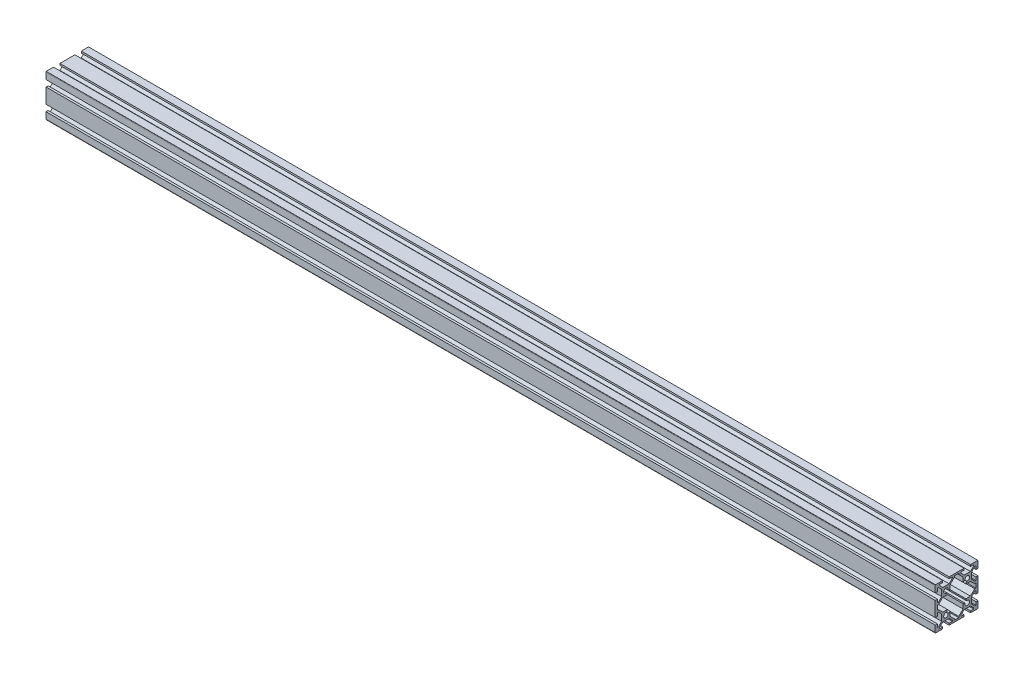
SolidWorks part; units mm, degrees
ref_plane "Front Plane" through (0, 0, 0) normal (0, 0, 1) x (1, 0, 0)
ref_plane "Top Plane" through (0, 0, 0) normal (0, 1, 0) x (1, 0, 0)
ref_plane "Right Plane" through (0, 0, 0) normal (1, 0, 0) x (0, 0, -1)
sketch "Sketch1" plane through (0, 0, 0) normal (1, 0, 0) x (0, 0, -1)
  line L0 (-16.9393, 2) -> (-18, 2)
  line L1 (-12.9393, 6) -> (-16.9393, 2)
  line L2 (-8.6667, 6) -> (-12.9393, 6)
  line L3 (-9.3359, 8.0078) -> (-8.6667, 6)
  line L4 (-6, 8.6667) -> (-8.0078, 9.3359)
  line L5 (-6, 12.9393) -> (-6, 8.6667)
  line L6 (-2, 16.9393) -> (-6, 12.9393)
  line L7 (-2, 18) -> (-2, 16.9393)
  line L8 (2, 18) -> (-2, 18)
  line L9 (2, 16.9393) -> (2, 18)
  line L10 (6, 12.9393) -> (2, 16.9393)
  line L11 (6, 8.6667) -> (6, 12.9393)
  line L12 (8.0078, 9.3359) -> (6, 8.6667)
  line L13 (8.6667, 6) -> (9.3359, 8.0078)
  line L14 (12.9393, 6) -> (8.6667, 6)
  line L15 (16.9393, 2) -> (12.9393, 6)
  line L16 (18, 2) -> (16.9393, 2)
  line L17 (18, -2) -> (18, 2)
  line L18 (16.9393, -2) -> (18, -2)
  line L19 (12.9393, -6) -> (16.9393, -2)
  line L20 (8.6667, -6) -> (12.9393, -6)
  line L21 (9.3359, -8.0078) -> (8.6667, -6)
  line L22 (6, -8.6667) -> (8.0078, -9.3359)
  line L23 (6, -12.9393) -> (6, -8.6667)
  line L24 (2, -16.9393) -> (6, -12.9393)
  line L25 (2, -18) -> (2, -16.9393)
  line L26 (-2, -18) -> (2, -18)
  line L27 (-2, -16.9393) -> (-2, -18)
  line L28 (-6, -12.9393) -> (-2, -16.9393)
  line L29 (-6, -8.6667) -> (-6, -12.9393)
  line L30 (-8.0078, -9.3359) -> (-6, -8.6667)
  line L31 (-8.6667, -6) -> (-9.3359, -8.0078)
  line L32 (-12.9393, -6) -> (-8.6667, -6)
  line L33 (-16.9393, -2) -> (-12.9393, -6)
  line L34 (-18, -2) -> (-16.9393, -2)
  line L35 (-18, 2) -> (-18, -2)
  line L36 (-20, 19) -> (-20, 13)
  line L37 (-20, 13) -> (-18, 13)
  line L38 (-18, 13) -> (-18, 16)
  line L39 (-18, 16) -> (-17.0607, 16)
  line L40 (-17.0607, 16) -> (-14, 12.9393)
  line L41 (-14, 12.9393) -> (-14, 7.0607)
  line L45 (-14, 7.0607) -> (-17.0607, 4)
  line L46 (-17.0607, 4) -> (-18, 4)
  line L47 (-18, 4) -> (-18, 7)
  line L48 (-18, 7) -> (-20, 7)
  line L49 (-20, 7) -> (-20, -7)
  line L50 (-20, -7) -> (-18, -7)
  line L51 (-18, -7) -> (-18, -4)
  line L52 (-18, -4) -> (-17.0607, -4)
  line L53 (-17.0607, -4) -> (-14, -7.0607)
  line L54 (-14, -7.0607) -> (-14, -12.9393)
  line L58 (-14, -12.9393) -> (-17.0607, -16)
  line L59 (-17.0607, -16) -> (-18, -16)
  line L60 (-18, -16) -> (-18, -13)
  line L61 (-18, -13) -> (-20, -13)
  line L62 (-20, -13) -> (-20, -19)
  line L63 (-19.8, -19.6) -> (-13, -19.6)
  line L64 (-13, -19.6) -> (-13, -18)
  line L65 (-13, -18) -> (-16, -18)
  line L66 (-16, -18) -> (-16, -17.0607)
  line L67 (-16, -17.0607) -> (-12.9393, -14)
  line L68 (-12.9393, -14) -> (-7.0607, -14)
  line L72 (-7.0607, -14) -> (-4, -17.0607)
  line L73 (-4, -17.0607) -> (-4, -18)
  line L74 (-4, -18) -> (-7, -18)
  line L75 (-7, -18) -> (-7, -19.6)
  line L76 (-7, -19.6) -> (7, -19.6)
  line L77 (7, -19.6) -> (7, -18)
  line L78 (7, -18) -> (4, -18)
  line L79 (4, -18) -> (4, -17.0607)
  line L80 (4, -17.0607) -> (7.0607, -14)
  line L81 (7.0607, -14) -> (12.9393, -14)
  line L85 (12.9393, -14) -> (16, -17.0607)
  line L86 (16, -17.0607) -> (16, -18)
  line L87 (16, -18) -> (13, -18)
  line L88 (13, -18) -> (13, -19.6)
  line L89 (13, -19.6) -> (19.8, -19.6)
  line L90 (20, -19) -> (20, -13)
  line L91 (20, -13) -> (18, -13)
  line L92 (18, -13) -> (18, -16)
  line L93 (18, -16) -> (17.0607, -16)
  line L94 (17.0607, -16) -> (14, -12.9393)
  line L98 (14, -12.9393) -> (14, -7.0607)
  line L99 (14, -7.0607) -> (17.0607, -4)
  line L100 (17.0607, -4) -> (18, -4)
  line L101 (18, -4) -> (18, -7)
  line L102 (18, -7) -> (20, -7)
  line L103 (20, -7) -> (20, 7)
  line L104 (20, 7) -> (18, 7)
  line L105 (18, 7) -> (18, 4)
  line L106 (18, 4) -> (17.0607, 4)
  line L107 (17.0607, 4) -> (14, 7.0607)
  line L111 (14, 7.0607) -> (14, 12.9393)
  line L112 (14, 12.9393) -> (17.0607, 16)
  line L113 (17.0607, 16) -> (18, 16)
  line L114 (18, 16) -> (18, 13)
  line L115 (18, 13) -> (20, 13)
  line L116 (20, 13) -> (20, 19)
  line L117 (19.8, 19.6) -> (13, 19.6)
  line L118 (13, 19.6) -> (13, 18)
  line L119 (13, 18) -> (16, 18)
  line L120 (16, 18) -> (16, 17.0607)
  line L121 (16, 17.0607) -> (12.9393, 14)
  line L125 (12.9393, 14) -> (7.0607, 14)
  line L126 (7.0607, 14) -> (4, 17.0607)
  line L127 (4, 17.0607) -> (4, 18)
  line L128 (4, 18) -> (7, 18)
  line L129 (7, 18) -> (7, 19.6)
  line L130 (7, 19.6) -> (-7, 19.6)
  line L131 (-7, 19.6) -> (-7, 18)
  line L132 (-7, 18) -> (-4, 18)
  line L133 (-4, 18) -> (-4, 17.0607)
  line L134 (-4, 17.0607) -> (-7.0607, 14)
  line L138 (-7.0607, 14) -> (-12.9393, 14)
  line L139 (-12.9393, 14) -> (-16, 17.0607)
  line L140 (-16, 17.0607) -> (-16, 18)
  line L141 (-16, 18) -> (-13, 18)
  line L142 (-13, 18) -> (-13, 19.6)
  line L143 (-13, 19.6) -> (-19.8, 19.6)
  arc A0 (-20, -19) -> (-19.8, -19.6) centre (-19, -19) ccw
  arc A1 (19.8, -19.6) -> (20, -19) centre (19, -19) ccw
  arc A2 (20, 19) -> (19.8, 19.6) centre (19, 19) ccw
  arc A3 (-19.8, 19.6) -> (-20, 19) centre (-19, 19) ccw
  arc A4 (-8.0078, 9.3359) -> (-9.3359, 8.0078) centre (-10, 10) ccw
  arc A5 (9.3359, 8.0078) -> (8.0078, 9.3359) centre (10, 10) ccw
  arc A6 (8.0078, -9.3359) -> (9.3359, -8.0078) centre (10, -10) ccw
  arc A7 (-9.3359, -8.0078) -> (-8.0078, -9.3359) centre (-10, -10) ccw
  dimension "A" = 40
  dimension "T" = 39.2
extrude "Boss-Extrude1" add sketch "Sketch1" along normal blind 832
ref_plane "Plane1" through (0, 19.6, 0) normal (0, 1, 0) x (1, 0, 0)
ref_plane "Plane2" through (0, 0, 0) normal (1, 0, 0) x (0, 0, -1)
ref_plane "Plane3" through (832, 0, 0) normal (1, 0, 0) x (0, 0, -1)
ref_plane "Plane4" through (7, 0, 0) normal (1, 0, 0) x (0, 0, -1)
ref_plane "Plane5" through (19, 0, 0) normal (1, 0, 0) x (0, 0, -1)
ref_plane "Plane6" through (31, 0, 0) normal (1, 0, 0) x (0, 0, -1)
ref_plane "Plane7" through (43, 0, 0) normal (1, 0, 0) x (0, 0, -1)
ref_plane "Plane8" through (55, 0, 0) normal (1, 0, 0) x (0, 0, -1)
sketch "Sketch2" [suppressed] plane through (7, 0, 0) normal (1, 0, 0) x (0, 0, -1)
  line L0 (10, -19.6) -> (12.75, -19.6)
  line L1 (12.75, -19.6) -> (12.75, 14)
  line L2 (12.75, 14) -> (14.75, 14)
  line L3 (14.75, 14) -> (14.75, 19.6)
  line L4 (14.75, 19.6) -> (10, 19.6)
  line L5 (10, 19.6) -> (10, -19.6) construction
  line L6 (10, 19.6) -> (10, -19.6)
  point P6 (10, 0)
  dimension "T" = 39.2
  dimension "FIX_3" = 5.6
  dimension "D1_s" = 9.5
  dimension "D_s" = 5.5
  dimension "FIX_4" = 10
revolve "Cut-Revolve1" [suppressed] cut sketch "Sketch2" angle 360 about L5
mirror "Mirror1" [suppressed] about plane through (0, 0, 0) normal (0, 0, 1)
sketch "Sketch3" [suppressed] plane through (18.5, 0, 0) normal (1, 0, 0) x (0, 0, -1)
  line L0 (10, -19.6) -> (12.75, -19.6)
  line L1 (12.75, -19.6) -> (12.75, 14)
  line L2 (12.75, 14) -> (14.75, 14)
  line L3 (14.75, 14) -> (14.75, 19.6)
  line L4 (14.75, 19.6) -> (10, 19.6)
  line L5 (10, 19.6) -> (10, -19.6) construction
  line L6 (10, 19.6) -> (10, -19.6)
  point P6 (10, 0)
  dimension "T" = 39.2
  dimension "FIX_6" = 5.6
  dimension "D1_s" = 9.5
  dimension "D_s" = 5.5
  dimension "FIX_7" = 10
revolve "Cut-Revolve2" [suppressed] cut sketch "Sketch3" angle 360 about L5
mirror "Mirror2" [suppressed] about plane through (0, 0, 0) normal (0, 0, 1)
sketch "Sketch4" [suppressed] plane through (30, 0, 0) normal (1, 0, 0) x (0, 0, -1)
  line L0 (10, -19.6) -> (12.75, -19.6)
  line L1 (12.75, -19.6) -> (12.75, 14)
  line L2 (12.75, 14) -> (14.75, 14)
  line L3 (14.75, 14) -> (14.75, 19.6)
  line L4 (14.75, 19.6) -> (10, 19.6)
  line L5 (10, 19.6) -> (10, -19.6) construction
  line L6 (10, 19.6) -> (10, -19.6)
  point P6 (10, 0)
  dimension "T" = 39.2
  dimension "FIX_9" = 5.6
  dimension "D1_s" = 9.5
  dimension "D_s" = 5.5
  dimension "FIX_10" = 10
revolve "Cut-Revolve3" [suppressed] cut sketch "Sketch4" angle 360 about L5
mirror "Mirror3" [suppressed] about plane through (0, 0, 0) normal (0, 0, 1)
sketch "Sketch5" [suppressed] plane through (41.5, 0, 0) normal (1, 0, 0) x (0, 0, -1)
  line L0 (10, -19.6) -> (12.75, -19.6)
  line L1 (12.75, -19.6) -> (12.75, 14)
  line L2 (12.75, 14) -> (14.75, 14)
  line L3 (14.75, 14) -> (14.75, 19.6)
  line L4 (14.75, 19.6) -> (10, 19.6)
  line L5 (10, 19.6) -> (10, -19.6) construction
  line L6 (10, 19.6) -> (10, -19.6)
  point P6 (10, 0)
  dimension "T" = 39.2
  dimension "FIX_12" = 5.6
  dimension "D1_s" = 9.5
  dimension "D_s" = 5.5
  dimension "FIX_13" = 10
revolve "Cut-Revolve4" [suppressed] cut sketch "Sketch5" angle 360 about L5
mirror "Mirror4" [suppressed] about plane through (0, 0, 0) normal (0, 0, 1)
sketch "Sketch6" [suppressed] plane through (53, 0, 0) normal (1, 0, 0) x (0, 0, -1)
  line L0 (10, -19.6) -> (12.75, -19.6)
  line L1 (12.75, -19.6) -> (12.75, 14)
  line L2 (12.75, 14) -> (14.75, 14)
  line L3 (14.75, 14) -> (14.75, 19.6)
  line L4 (14.75, 19.6) -> (10, 19.6)
  line L5 (10, 19.6) -> (10, -19.6) construction
  line L6 (10, 19.6) -> (10, -19.6)
  point P6 (10, 0)
  dimension "T" = 39.2
  dimension "FIX_15" = 5.6
  dimension "D1_s" = 9.5
  dimension "D_s" = 5.5
  dimension "FIX_16" = 10
revolve "Cut-Revolve5" [suppressed] cut sketch "Sketch6" angle 360 about L5
mirror "Mirror5" [suppressed] about plane through (0, 0, 0) normal (0, 0, 1)
sketch "Sketch7" [suppressed] plane through (0, 19.6, 0) normal (0, 1, 0) x (1, 0, 0)
  circle A0 centre (7, -10) radius 3.675
  circle A1 centre (7, 10) radius 3.675
  dimension "D" = 7.35
  dimension "AV" = 7
  dimension "FIX_18" = 20
  dimension "FIX_19" = 10
extrude "Cut-Extrude1" [suppressed] cut sketch "Sketch7" against normal blind 39.2
sketch "Sketch8" [suppressed] plane through (0, 19.6, 0) normal (0, 1, 0) x (1, 0, 0)
  circle A0 centre (18.5, -10) radius 3.675
  circle A1 centre (18.5, 10) radius 3.675
  dimension "D" = 7.35
  dimension "BV" = 19
  dimension "FIX_20" = 10
  dimension "FIX_21" = 20
extrude "Cut-Extrude2" [suppressed] cut sketch "Sketch8" against normal blind 39.2
sketch "Sketch9" [suppressed] plane through (0, 19.6, 0) normal (0, 1, 0) x (1, 0, 0)
  circle A0 centre (30, -10) radius 3.675
  circle A1 centre (30, 10) radius 3.675
  dimension "D" = 7.35
  dimension "CV" = 31
  dimension "FIX_22" = 20
  dimension "FIX_23" = 10
extrude "Cut-Extrude3" [suppressed] cut sketch "Sketch9" against normal blind 39.2
sketch "Sketch10" [suppressed] plane through (0, 19.6, 0) normal (0, 1, 0) x (1, 0, 0)
  circle A0 centre (41.5, -10) radius 3.675
  circle A1 centre (41.5, 10) radius 3.675
  dimension "D" = 7.35
  dimension "DV" = 43
  dimension "FIX_24" = 10
  dimension "FIX_25" = 20
extrude "Cut-Extrude4" [suppressed] cut sketch "Sketch10" against normal blind 39.2
sketch "Sketch11" [suppressed] plane through (0, 19.6, 0) normal (0, 1, 0) x (1, 0, 0)
  circle A0 centre (53, -10) radius 3.675
  circle A1 centre (53, 10) radius 3.675
  dimension "D" = 7.35
  dimension "EV" = 55
  dimension "FIX_26" = 10
  dimension "FIX_27" = 20
extrude "Cut-Extrude5" [suppressed] cut sketch "Sketch11" against normal blind 39.2
sketch "Sketch12" [suppressed] plane through (0, 0, 0) normal (1, 0, 0) x (0, 0, -1)
  circle A0 centre (-10, -10) radius 2.1
  circle A1 centre (10, -10) radius 2.1
  circle A2 centre (10, 10) radius 2.1
  circle A3 centre (-10, 10) radius 2.1
  dimension "FIX_28" = 4.2
  dimension "FIX_29" = 20
  dimension "FIX_30" = 20
  dimension "FIX_31" = 10
  dimension "FIX_32" = 10
extrude "Boss-Extrude2" [suppressed] add sketch "Sketch12" along normal blind 15
hole_wizard "Tapped Hole1" [suppressed] positions "Sketch14" profile "Sketch13" tap size "M5x0.8" standard "JIS"
sketch "Sketch14" [suppressed] plane through (0, 0, 0) normal (1, 0, 0) x (0, 0, -1)
  point P0 (10, 10)
  point P2 (-10, 10)
  point P4 (10, -10)
  point P6 (-10, -10)
  dimension "FIX_34" = 20
  dimension "FIX_35" = 20
  dimension "FIX_36" = 10
  dimension "FIX_37" = 10
sketch "Sketch13" [suppressed] plane through (0, 10, -10) normal (0, 1, 0) x (0, 0, 1)
  line L0 (0, 0) -> (0, 15)
  line L1 (0, 15) -> (2.1, 15)
  line L2 (2.1, 15) -> (2.1, 0)
  line L5 (2.1, 0) -> (0, 0)
  line L11 (0, -6.35) -> (0, 107.95) construction
  dimension "Thru Tap Drill Dia." = 4.2
  dimension "Thru Tap Drill Depth" = 15
cosmetic thread "Hole Thread1" [suppressed] parameters "NFIX_2"=15, "NFIX_1"=5
cosmetic thread "Hole Thread2" [suppressed] parameters "NFIX_2"=15, "NFIX_1"=5
cosmetic thread "Hole Thread3" [suppressed] parameters "NFIX_2"=15, "NFIX_1"=5
cosmetic thread "Hole Thread4" [suppressed] parameters "NFIX_2"=15, "NFIX_1"=5
sketch "Sketch15" [suppressed] plane through (100, 0, 0) normal (1, 0, 0) x (0, 0, -1)
  circle A0 centre (-10, -10) radius 2.1
  circle A1 centre (10, -10) radius 2.1
  circle A2 centre (10, 10) radius 2.1
  circle A3 centre (-10, 10) radius 2.1
  dimension "FIX_39" = 4.2
  dimension "FIX_38" = 20
  dimension "FIX_40" = 10
  dimension "FIX_41" = 10
  dimension "FIX_42" = 20
extrude "Boss-Extrude3" [suppressed] add sketch "Sketch15" against normal blind 15
hole_wizard "Tapped Hole2" [suppressed] positions "Sketch17" profile "Sketch16" tap size "M5x0.8" standard "JIS"
sketch "Sketch17" [suppressed] plane through (100, 0, 0) normal (1, 0, 0) x (0, 0, -1)
  point P0 (-10, 10)
  point P2 (10, 10)
  point P4 (-10, -10)
  point P6 (10, -10)
  dimension "FIX_44" = 20
  dimension "FIX_45" = 20
  dimension "FIX_46" = 10
  dimension "FIX_47" = 10
sketch "Sketch16" [suppressed] plane through (100, 10, 10) normal (0, 1, 0) x (0, 0, -1)
  line L0 (0, 0) -> (0, 15)
  line L1 (0, 15) -> (2.1, 15)
  line L2 (2.1, 15) -> (2.1, 0)
  line L5 (2.1, 0) -> (0, 0)
  line L11 (0, -6.35) -> (0, 107.95) construction
  dimension "Thru Tap Drill Dia." = 4.2
  dimension "Thru Tap Drill Depth" = 15
cosmetic thread "Hole Thread5" [suppressed] parameters "NFIX_2"=15, "NFIX_1"=5
cosmetic thread "Hole Thread6" [suppressed] parameters "NFIX_2"=15, "NFIX_1"=5
cosmetic thread "Hole Thread7" [suppressed] parameters "NFIX_2"=15, "NFIX_1"=5
cosmetic thread "Hole Thread8" [suppressed] parameters "NFIX_2"=15, "NFIX_1"=5
sketch "Sketch18" [suppressed] plane through (0, 0, 0) normal (1, 0, 0) x (0, 0, -1)
  circle A1 centre (-10, -10) radius 2.1
  circle A2 centre (10, -10) radius 2.1
  circle A3 centre (10, 10) radius 2.1
  circle A4 centre (-10, 10) radius 2.1
  dimension "FIX_48" = 4.2
  dimension "FIX_49" = 20
  dimension "FIX_50" = 20
  dimension "FIX_51" = 10
  dimension "FIX_52" = 10
extrude "Boss-Extrude4" [suppressed] add sketch "Sketch18" along normal blind 15
sketch "Sketch19" [suppressed] plane through (100, 0, 0) normal (1, 0, 0) x (0, 0, -1)
  circle A0 centre (-10, -10) radius 2.1
  circle A1 centre (10, -10) radius 2.1
  circle A2 centre (10, 10) radius 2.1
  circle A3 centre (-10, 10) radius 2.1
  dimension "FIX_56" = 4.2
  dimension "FIX_54" = 20
  dimension "FIX_55" = 20
  dimension "FIX_57" = 10
  dimension "FIX_58" = 10
extrude "Boss-Extrude5" [suppressed] add sketch "Sketch19" against normal blind 15
hole_wizard "Tapped Hole3" [suppressed] positions "Sketch21" profile "Sketch20" tap size "M5x0.8" standard "JIS"
sketch "Sketch21" [suppressed] plane through (0, 0, 0) normal (1, 0, 0) x (0, 0, -1)
  point P0 (10, 10)
  point P2 (-10, 10)
  point P4 (-10, -10)
  point P6 (10, -10)
  dimension "FIX_60" = 20
  dimension "FIX_61" = 10
  dimension "FIX_62" = 20
  dimension "FIX_63" = 10
sketch "Sketch20" [suppressed] plane through (0, 10, -10) normal (0, 1, 0) x (0, 0, 1)
  line L0 (0, 0) -> (0, 15)
  line L1 (0, 15) -> (2.1, 15)
  line L2 (2.1, 15) -> (2.1, 0)
  line L5 (2.1, 0) -> (0, 0)
  line L11 (0, -6.35) -> (0, 107.95) construction
  dimension "Thru Tap Drill Dia." = 4.2
  dimension "Thru Tap Drill Depth" = 15
cosmetic thread "Hole Thread9" [suppressed] parameters "NFIX_2"=15, "NFIX_1"=5
cosmetic thread "Hole Thread10" [suppressed] parameters "NFIX_2"=15, "NFIX_1"=5
cosmetic thread "Hole Thread11" [suppressed] parameters "NFIX_2"=15, "NFIX_1"=5
cosmetic thread "Hole Thread12" [suppressed] parameters "NFIX_2"=15, "NFIX_1"=5
hole_wizard "Tapped Hole4" [suppressed] positions "Sketch23" profile "Sketch22" tap size "M5x0.8" standard "JIS"
sketch "Sketch23" [suppressed] plane through (100, 0, 0) normal (1, 0, 0) x (0, 0, -1)
  point P0 (-10, 10)
  point P2 (10, 10)
  point P4 (-10, -10)
  point P6 (10, -10)
  dimension "FIX_64" = 20
  dimension "FIX_65" = 20
  dimension "FIX_66" = 10
  dimension "FIX_67" = 10
sketch "Sketch22" [suppressed] plane through (100, 10, 10) normal (0, 1, 0) x (0, 0, -1)
  line L0 (0, 0) -> (0, 15)
  line L1 (0, 15) -> (2.1, 15)
  line L2 (2.1, 15) -> (2.1, 0)
  line L5 (2.1, 0) -> (0, 0)
  line L11 (0, -6.35) -> (0, 107.95) construction
  dimension "Thru Tap Drill Dia." = 4.2
  dimension "Thru Tap Drill Depth" = 15
cosmetic thread "Hole Thread13" [suppressed] parameters "NFIX_2"=15, "NFIX_1"=5
cosmetic thread "Hole Thread14" [suppressed] parameters "NFIX_2"=15, "NFIX_1"=5
cosmetic thread "Hole Thread15" [suppressed] parameters "NFIX_2"=15, "NFIX_1"=5
cosmetic thread "Hole Thread16" [suppressed] parameters "NFIX_2"=15, "NFIX_1"=5
